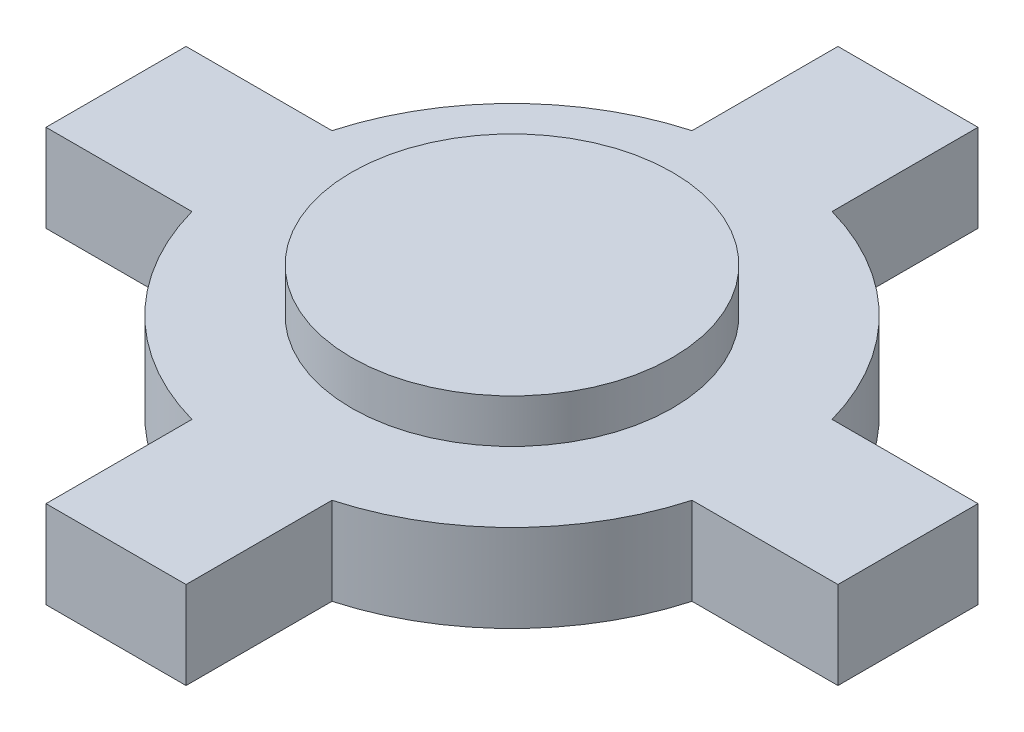
SolidWorks part; units mm, degrees
ref_plane "前视基准面" through (0, 0, 0) normal (0, 0, 1) x (1, 0, 0)
ref_plane "上视基准面" through (0, 0, 0) normal (0, 1, 0) x (1, 0, 0)
ref_plane "右视基准面" through (0, 0, 0) normal (1, 0, 0) x (0, 0, -1)
other "Configuration Table"
sketch "草图1" plane through (0, 0, 0) normal (0, 1, 0) x (1, 0, 0)
  line L0 (0, 7.9747) -> (0, -8.6444) construction
  line L1 (-13.5703, 2.4) -> (-8.5703, 2.4)
  line L2 (-13.5703, 2.4) -> (-13.5703, -2.4)
  line L3 (-13.5703, -2.4) -> (-8.5703, -2.4)
  line L4 (13.5703, 2.4) -> (13.5703, -2.4)
  line L5 (-2.4, 13.5703) -> (2.4, 13.5703)
  line L6 (-2.4, 13.5703) -> (-2.4, 8.5703)
  line L7 (-2.4, -13.5703) -> (2.4, -13.5703)
  line L8 (2.4, 13.5703) -> (2.4, 8.5703)
  line L13 (-10.8789, 0) -> (11.1113, 0) construction
  line L15 (-2.4, -8.5703) -> (-2.4, -13.5703)
  line L16 (8.5703, 2.4) -> (13.5703, 2.4)
  line L17 (8.5703, -2.4) -> (13.5703, -2.4)
  line L18 (2.4, -8.5703) -> (2.4, -13.5703)
  arc A0 (-2.4, 8.5703) -> (-8.5703, 2.4) centre (0, 0) ccw
  arc A1 (8.5703, 2.4) -> (2.4, 8.5703) centre (0, 0) ccw
  arc A2 (2.4, -8.5703) -> (8.5703, -2.4) centre (0, 0) ccw
  arc A3 (-8.5703, -2.4) -> (-2.4, -8.5703) centre (0, 0) ccw
  dimension "D1" = 17.8
  dimension "D2" = 4.8
  dimension "D3" = 5
extrude "凸台-拉伸1" add sketch "草图1" along normal blind 3
sketch "草图2" plane through (0, 3, 0) normal (0, 1, 0) x (1, 0, 0)
  circle A0 centre (0, 0) radius 5.5
  dimension "D1" = 11
extrude "凸台-拉伸2" add sketch "草图2" along normal blind 1.5
